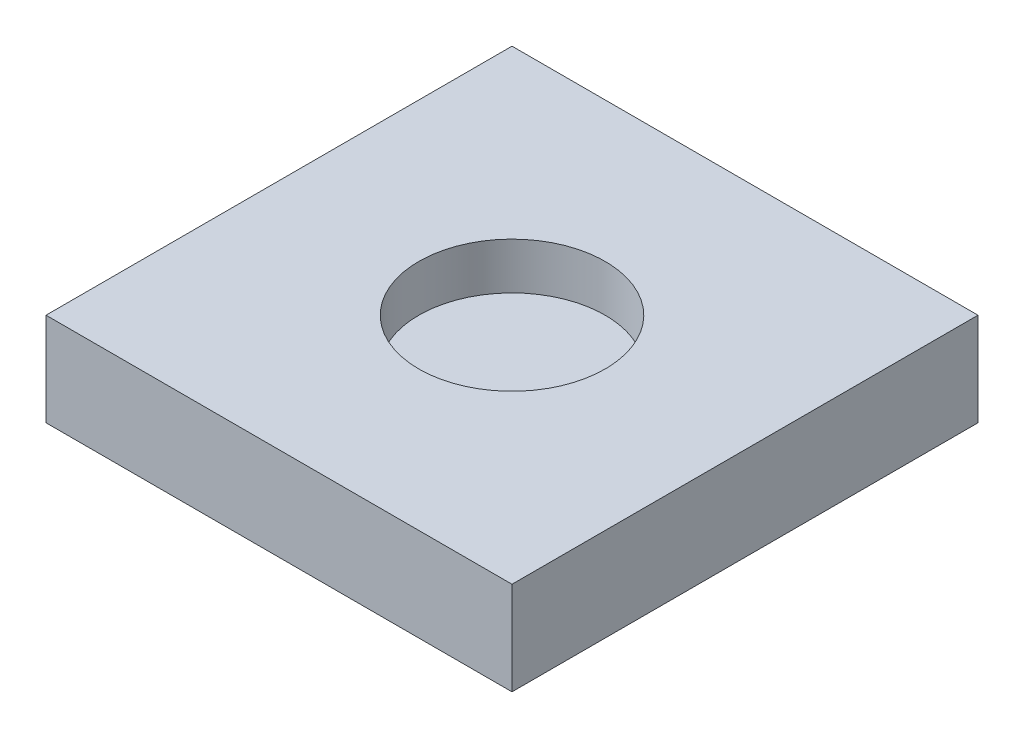
SolidWorks part; units mm, degrees
material "1060 合金"
ref_plane "前视基准面" through (0, 0, 0) normal (0, 0, 1) x (1, 0, 0)
ref_plane "上视基准面" through (0, 0, 0) normal (0, 1, 0) x (1, 0, 0)
ref_plane "右视基准面" through (0, 0, 0) normal (1, 0, 0) x (0, 0, -1)
sketch "草图1" plane through (0, 0, 0) normal (0, 0, 1) x (1, 0, 0)
  line L0 (0, 181.0531) -> (0, -174.4015) construction
  line L2 (-250, -50) -> (250, -50)
  line L3 (-250, -50) -> (-250, 50)
  line L4 (-250, 50) -> (250, 50)
  line L5 (250, -50) -> (250, 50)
  line L6 (-250, -50) -> (250, 50) construction
  line L7 (-250, 50) -> (250, -50) construction
  point P3 (0, 0)
  dimension "D1" = 500
  dimension "D2" = 100
extrude "凸台-拉伸1" add sketch "草图1" along normal mid plane 500
sketch "草图2" plane through (0, 50, 0) normal (0, 1, 0) x (1, 0, 0)
  circle A0 centre (0, 0) radius 100
  dimension "D1" = 200
extrude "切除-拉伸1" cut sketch "草图2" against normal blind 50
